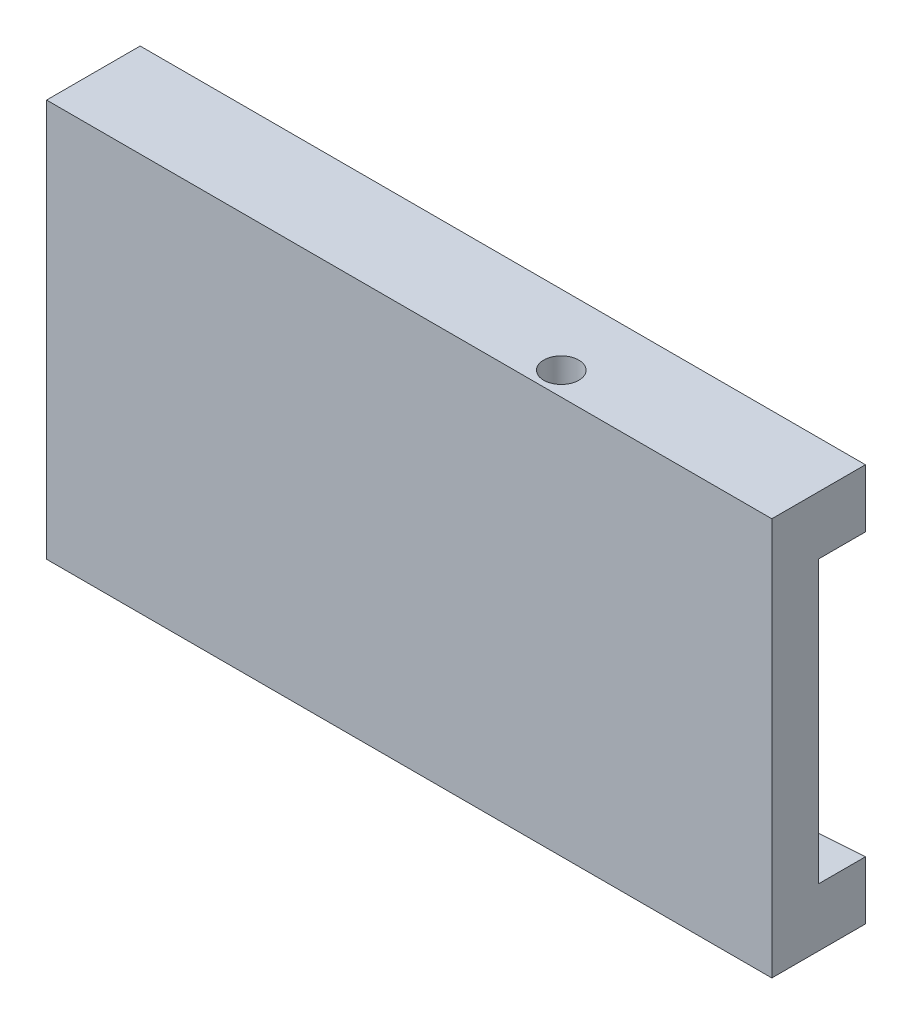
SolidWorks part; units mm, degrees
ref_plane "Front Plane" through (0, 0, 0) normal (0, 0, 1) x (1, 0, 0)
ref_plane "Top Plane" through (0, 0, 0) normal (0, 1, 0) x (1, 0, 0)
ref_plane "Right Plane" through (0, 0, 0) normal (1, 0, 0) x (0, 0, -1)
sketch "Sketch1" plane through (0, 0, 0) normal (0, 1, 0) x (1, 0, 0)
  line L1 (-20, 2) -> (20, 2)
  line L2 (-20, 2) -> (-20, -2)
  line L3 (-20, -2) -> (20, -2)
  line L4 (20, 2) -> (20, -2)
  line L5 (-20, 2) -> (20, -2) construction
  line L6 (-20, -2) -> (20, 2) construction
  point P0 (0, 0)
  dimension "D1" = 4
  dimension "D2" = 40
extrude "Boss-Extrude1" add sketch "Sketch1" along normal blind 34
sketch "Sketch2" plane through (0, 0, 0) normal (0, -1, 0) x (1, 0, 0)
  circle A0 centre (0, 0) radius 1.5
  dimension "D1" = 3
extrude "Cut-Extrude1" cut sketch "Sketch2" against normal blind 6
ref_plane "Plane1" through (0, 17, 0) normal (0, -1, 0) x (-1, 0, 0)
mirror "Mirror1" about plane through (0, 17, 0) normal (0, -1, 0) of "Cut-Extrude1"
sketch "Sketch3" plane through (-20, 0, 0) normal (-1, 0, 0) x (0, 0, 1)
  line L4 (-2, 0) -> (2, 0)
  line L5 (2, 0) -> (2, 34)
  line L6 (2, 34) -> (-2, 34)
  line L7 (-2, 34) -> (-2, 0)
  line L8 (-2, 0) -> (2, 0)
  line L9 (2, 0) -> (2, 34)
  line L10 (2, 34) -> (-2, 34)
  line L11 (-2, 34) -> (-2, 0)
  dimension "D1" = 0
extrude "Boss-Extrude2" add sketch "Sketch3" along normal blind 22
sketch "Sketch4" plane through (0, 0, 0) normal (0, -1, 0) x (1, 0, 0)
  circle A0 centre (-35.884, 0) radius 1.5
  circle A1 centre (0, 0) radius 1.5 construction
extrude "Cut-Extrude2" [suppressed] cut sketch "Sketch4" against normal blind 8
sketch "Sketch5" plane through (0, 0, -2) normal (0, 0, -1) x (-1, 0, 0)
  line L0 (-20, 29.0246) -> (42, 33)
  line L1 (-20, 34) -> (-20, 0) construction
  line L2 (42, 34) -> (42, 0) construction
  line L3 (42, 33) -> (42, 34)
  line L4 (42, 34) -> (-20, 34)
  line L5 (-20, 34) -> (-20, 29.0246)
  line L6 (-2.2, 17) -> (2.2, 17) construction
  line L7 (42, 0) -> (-20, 0)
  line L8 (42, 1) -> (42, 0)
  line L9 (-20, 4.9754) -> (42, 1)
  line L10 (-20, 0) -> (-20, 4.9754)
  point P16 (0, 0)
  point P17 (42, 29.4202)
  dimension "D1" = 24
  dimension "D2" = 32
extrude "Boss-Extrude3" add sketch "Sketch5" along normal blind 4
